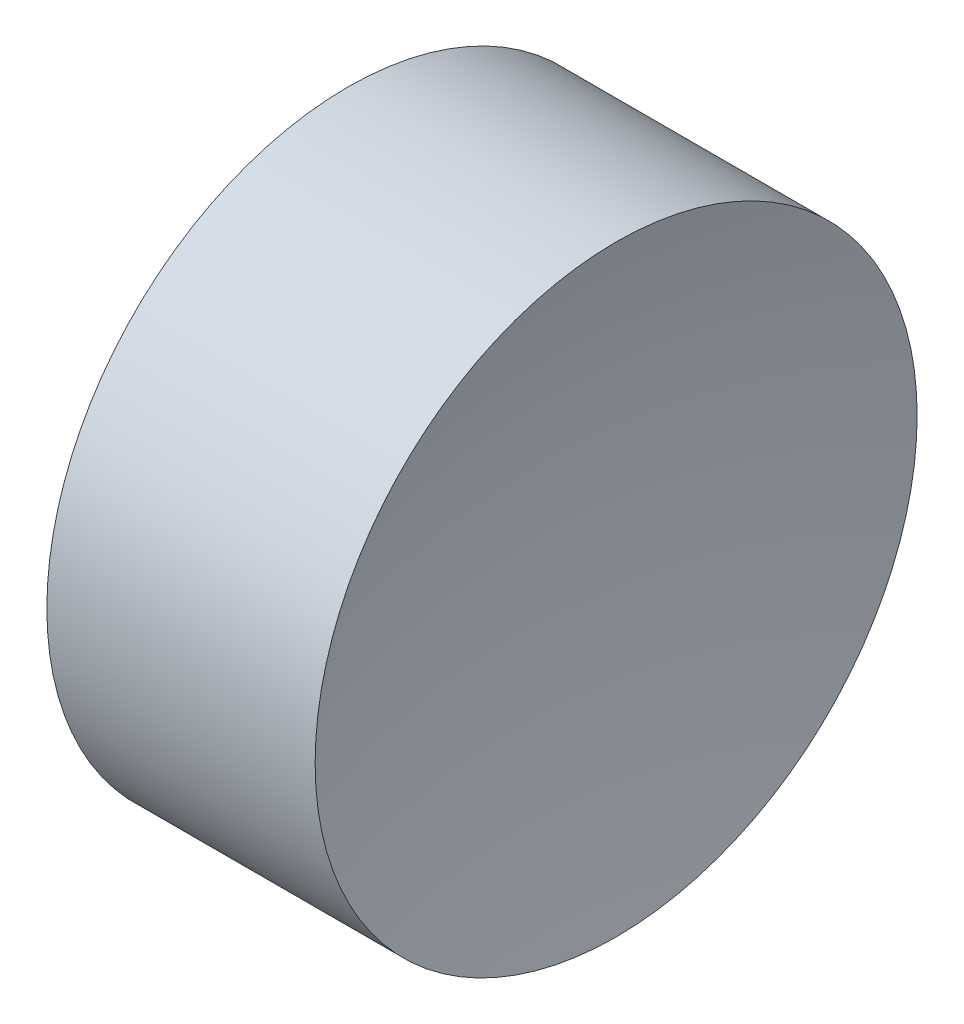
SolidWorks part; units mm, degrees
ref_plane "前视基准面" through (0, 0, 0) normal (0, 0, 1) x (1, 0, 0)
ref_plane "上视基准面" through (0, 0, 0) normal (0, 1, 0) x (1, 0, 0)
ref_plane "右视基准面" through (0, 0, 0) normal (1, 0, 0) x (0, 0, -1)
sketch "草图1" plane through (0, 0, 0) normal (0, 0, 1) x (1, 0, 0)
  line L0 (10.6125, 6.5223) -> (13.9161, 6.5223) construction
  line L1 (12.5141, 6.5223) -> (11.5141, 6.5223)
  line L3 (12.0141, 8.0223) -> (12.6802, 8.0223)
  line L4 (12.0141, 8.0223) -> (11.3433, 8.0223)
  arc A0 (12.6802, 8.0223) -> (12.5141, 6.5223) centre (19.1841, 6.5431) ccw
  arc A1 (11.5141, 6.5223) -> (11.3433, 8.0223) centre (4.8441, 6.5223) ccw
revolve "旋转1" add sketch "草图1" angle 360 about L0
